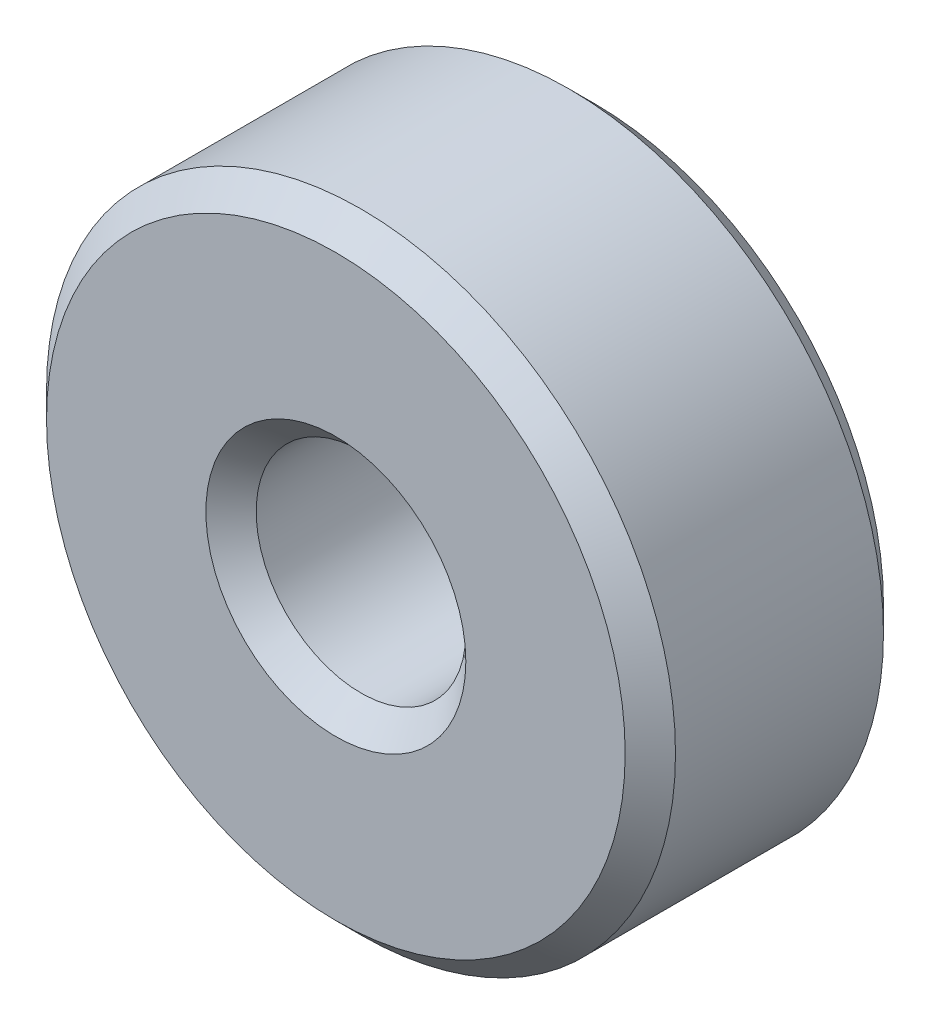
SolidWorks part; units mm, degrees
ref_plane "Front Plane" through (0, 0, 0) normal (0, 0, 1) x (1, 0, 0)
ref_plane "Top Plane" through (0, 0, 0) normal (0, 1, 0) x (1, 0, 0)
ref_plane "Right Plane" through (0, 0, 0) normal (1, 0, 0) x (0, 0, -1)
sketch "Sketch1" plane through (0, 0, 0) normal (0, 0, 1) x (1, 0, 0)
  circle A0 centre (0, 0) radius 1.5875
  circle A1 centre (0, 0) radius 4.7625
  dimension "D1" = 3.175
  dimension "D2" = 9.525
extrude "Boss-Extrude1" add sketch "Sketch1" along normal blind 3.9116
chamfer "Chamfer1" distance 0.381 angle 45 4 edges at (1.5875, 0, 0) (4.7625, 0, 0) (4.7625, 0, 3.9116) (1.5875, 0, 3.9116)
